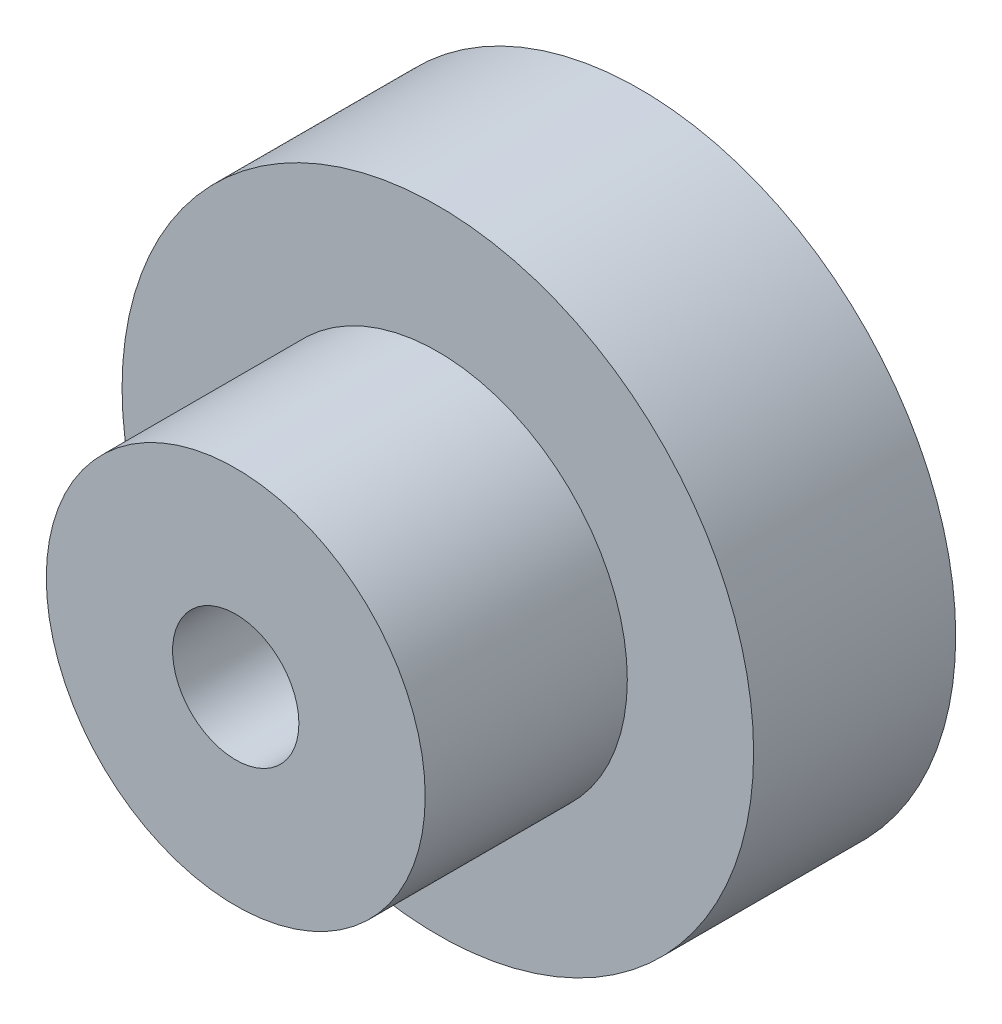
SolidWorks part; units mm, degrees
ref_plane "Front" through (0, 0, 0) normal (0, 0, 1) x (1, 0, 0)
ref_plane "Top" through (0, 0, 0) normal (0, 1, 0) x (1, 0, 0)
ref_plane "Right" through (0, 0, 0) normal (1, 0, 0) x (0, 0, -1)
sketch "Эскиз1" plane through (0, 0, 0) normal (0, 0, 1) x (1, 0, 0)
  circle A0 centre (0, 0) radius 2.5
  circle A1 centre (0, 0) radius 12.5
  dimension "D1" = 5
  dimension "D2" = 25
extrude "Бобышка-Вытянуть1" add sketch "Эскиз1" along normal blind 8
sketch "Эскиз2" plane through (0, 0, 8) normal (0, 0, 1) x (1, 0, 0)
  circle A0 centre (0, 0) radius 7.5
  circle A1 centre (0, 0) radius 2.5 construction
  circle A2 centre (0, 0) radius 2.5
  dimension "D1" = 15
extrude "Бобышка-Вытянуть2" add sketch "Эскиз2" along normal blind 8
sketch "Эскиз4" plane through (0, 0, 0) normal (1, 0, 0) x (0, 0, -1)
  line L0 (-16, 7.5) -> (-16, -7.5) construction
  line L1 (-16, 7.5) -> (-16, -7.5)
  line L2 (-8, 7.5) -> (-8, -7.5) construction
  line L3 (-8, 7.5) -> (-8, -7.5)
  line L4 (-16, 0) -> (0, 0) construction
  circle A0 centre (-11, 0) radius 1.5
  dimension "D1" = 3
  dimension "D2" = 5
extrude "Вырез-Вытянуть1" cut sketch "Эскиз4" against normal blind 10 contours A0 L4 | L4 A0
